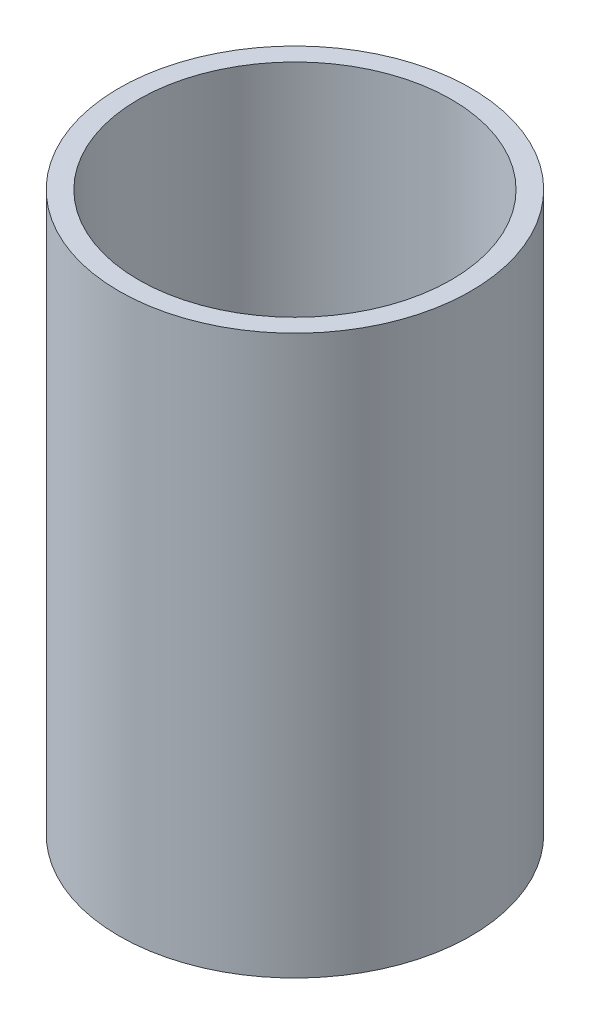
SolidWorks part; units mm, degrees
ref_plane "Plan de face" through (0, 0, 0) normal (0, 0, 1) x (1, 0, 0)
ref_plane "Plan de dessus" through (0, 0, 0) normal (0, 1, 0) x (1, 0, 0)
ref_plane "Plan de droite" through (0, 0, 0) normal (1, 0, 0) x (0, 0, -1)
sketch "Esquisse1" plane through (0, 0, 0) normal (0, 1, 0) x (1, 0, 0)
  circle A0 centre (0, 0) radius 31.5
extrude "Boss.-Extru.1" add sketch "Esquisse1" along normal blind 100
sketch "Esquisse2" plane through (0, 100, 0) normal (0, 1, 0) x (1, 0, 0)
  circle A0 centre (0, 0) radius 28
extrude "Enlèv. mat.-Extru.1" cut sketch "Esquisse2" against normal up to next
